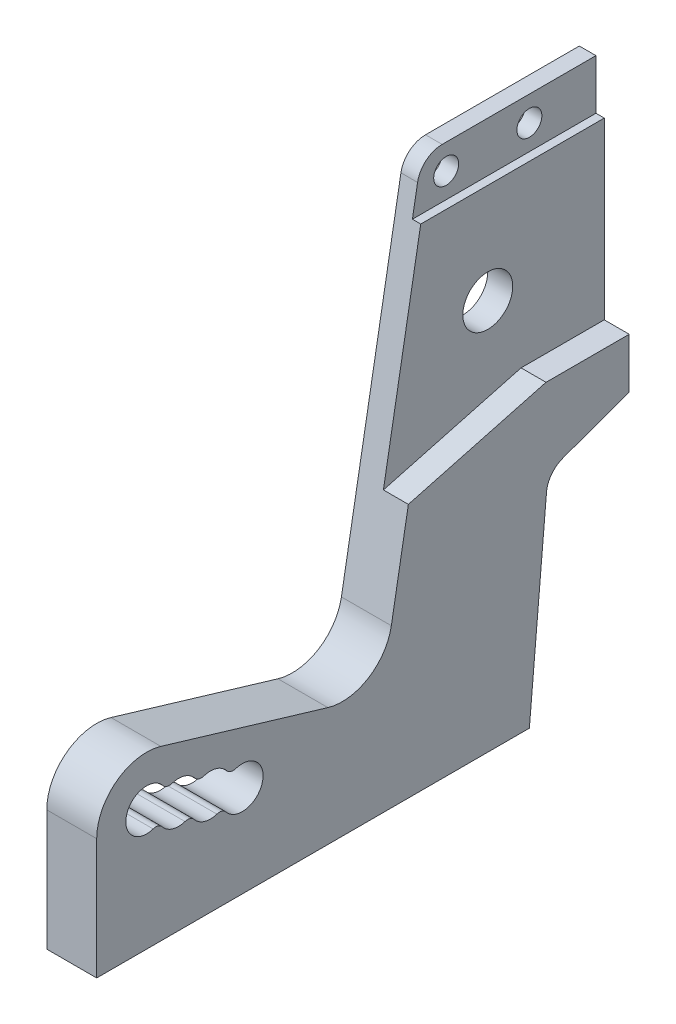
SolidWorks part; units mm, degrees
material "1060 Alloy"
ref_plane "Front Plane" through (0, 0, 0) normal (0, 0, 1) x (1, 0, 0)
ref_plane "Top Plane" through (0, 0, 0) normal (0, 1, 0) x (1, 0, 0)
ref_plane "Right Plane" through (0, 0, 0) normal (1, 0, 0) x (0, 0, -1)
sketch "Sketch1" plane through (0, 0, 0) normal (1, 0, 0) x (0, 0, -1)
  line L1 (0, 0) -> (64, 0)
  line L2 (0, 0) -> (0, 62)
  line L3 (0, 62) -> (64, 62)
  line L4 (64, 0) -> (64, 62)
  circle A0 centre (6, 14.5) radius 2.5
  circle A1 centre (50, 44) radius 3
  dimension "D1" = 6
  dimension "D2" = 5
  dimension "D3" = 14.5
  dimension "D4" = 6
  dimension "D5" = 44
  dimension "D6" = 50
  dimension "D7" = 64
  dimension "D8" = 62
extrude "Boss-Extrude1" add sketch "Sketch1" along normal blind 6
sketch "Sketch3" plane through (6, 0, 0) normal (1, 0, 0) x (0, 0, -1)
  line L57 (64, 0) -> (52, 0)
  line L58 (64, 0) -> (64, 29)
  line L59 (64, 29) -> (54.2259, 25.4425)
  line L60 (52, 0) -> (54.2259, 25.4425)
  dimension "D1" = 70
  dimension "D2" = 29
  dimension "D3" = 52
  dimension "D4" = 85
extrude "Cut-Extrude2" cut sketch "Sketch3" against normal up to next
fillet "Fillet2" radius 3 1 edges at (3, 25.4425, -54.2259)
hole_wizard "Tap Drill for M3 Tap1" positions "Sketch5" profile "Sketch4" hole size "M3" standard "ISO"
sketch "Sketch5" plane through (0, 0, 0) normal (0, -1, 0) x (-1, 0, 0)
  line L0 (0, 0) -> (0, 52) construction
  line L1 (-6, 0) -> (0, 0) construction
  point P0 (-3, 48)
  point P2 (-3, 12)
  dimension "D1" = 3
  dimension "D2" = 12
  dimension "D3" = 36
sketch "Sketch4" plane through (3, 0, -48) normal (1, 0, 0) x (0, 0, -1)
  line L0 (0, 0) -> (0, 9.7511)
  line L1 (0, 9.7511) -> (1.25, 9)
  line L2 (1.25, 9) -> (1.25, 0)
  line L5 (1.25, 0) -> (0, 0)
  line L10 (0, 9.7511) -> (-1.25, 9) construction
  line L11 (0, -6.35) -> (0, 107.95) construction
  dimension "Hole Dia." = 2.5
  dimension "Hole Depth" = 9
  dimension "Drill Angle" = 118
sketch "Sketch9" plane through (6, 0, 0) normal (1, 0, 0) x (0, 0, -1)
  line L0 (7.7183, 20.2487) -> (27.7834, 14.2513)
  line L1 (0, 0) -> (52, 0) construction
  line L19 (43, 62) -> (35.4106, 18.9581)
  line L21 (0, 62) -> (0, 0) construction
  line L22 (43, 62) -> (0, 62)
  line L23 (0, 62) -> (0, 14.5)
  line L24 (0, 62) -> (0, 0) construction
  line L25 (64, 62) -> (0, 62) construction
  arc A0 (35.4106, 18.9581) -> (27.7834, 14.2513) centre (29.5017, 20) cw
  arc A12 (0, 14.5) -> (7.7183, 20.2487) centre (6, 14.5) cw
  circle A16 centre (6, 14.5) radius 2.5 construction
  dimension "D1" = 43
  dimension "D2" = 80
  dimension "D3" = 20
extrude "Cut-Extrude3" cut sketch "Sketch9" against normal blind 8
sketch "Sketch13" plane through (6, 0, 0) normal (1, 0, 0) x (0, 0, -1)
  line L0 (64, 29) -> (64, 62) construction
  line L1 (54, 35) -> (64, 35)
  line L2 (64, 62) -> (43, 62) construction
  line L3 (64, 62) -> (43, 62)
  line L4 (64, 35) -> (64, 62)
  line L5 (35.4106, 18.9581) -> (43, 62) construction
  line L11 (43, 62) -> (37.4576, 30.5675)
  line L15 (37.4576, 30.5675) -> (54, 35)
  dimension "D1" = 10
  dimension "D2" = 65
  dimension "D3" = 27
extrude "Cut-Extrude4" cut sketch "Sketch13" against normal blind 3
fillet "Fillet3" radius 3 1 edges at (1.5, 62, -43)
sketch "Sketch14" plane through (3, 0, 0) normal (1, 0, 0) x (0, 0, -1)
  line L0 (64, 35) -> (64, 62) construction
  line L1 (64, 62) -> (45.5173, 62) construction
  circle A0 centre (56, 59) radius 1.5
  circle A1 centre (46, 59) radius 1.5
  dimension "D1" = 3
  dimension "D2" = 10
  dimension "D3" = 8
  dimension "D4" = 3
extrude "Cut-Extrude5" cut sketch "Sketch14" against normal up to next
sketch "Sketch15" plane through (0, 0, 0) normal (-1, 0, 0) x (0, 0, 1)
  line L0 (-6, 14.5) -> (-26.0652, 8.5026) construction
  line L1 (-27.7834, 14.2513) -> (-7.7183, 20.2487) construction
  circle A0 centre (-9.8325, 13.3545) radius 2.5
  circle A1 centre (-6, 14.5) radius 2.5 construction
  dimension "D1" = 4
extrude "Cut-Extrude6" cut sketch "Sketch15" against normal up to next (6 mm away)
pattern_linear "LPattern3" count 3 spacing 4 along (0, -0.2864, -0.9581) of "Cut-Extrude6"
fillet "Fillet4" radius 1 6 edges at (3, 12.4901, -7.4867) (3, 15.3644, -8.3458) (3, 11.3446, -11.3191) (3, 14.2189, -12.1783) (3, 13.0734, -16.0107) (3, 10.1991, -15.1516)
sketch "Sketch16" plane through (3, 0, 0) normal (1, 0, 0) x (0, 0, -1)
  line L0 (42.5629, 59.5209) -> (37.4576, 30.5675) construction
  line L1 (64, 62) -> (41.942, 62)
  line L2 (64, 62) -> (64, 56)
  line L3 (64, 56) -> (41.942, 56)
  line L4 (41.942, 62) -> (41.942, 56)
  dimension "D1" = 6
extrude "Cut-Extrude7" cut sketch "Sketch16" against normal blind 1
